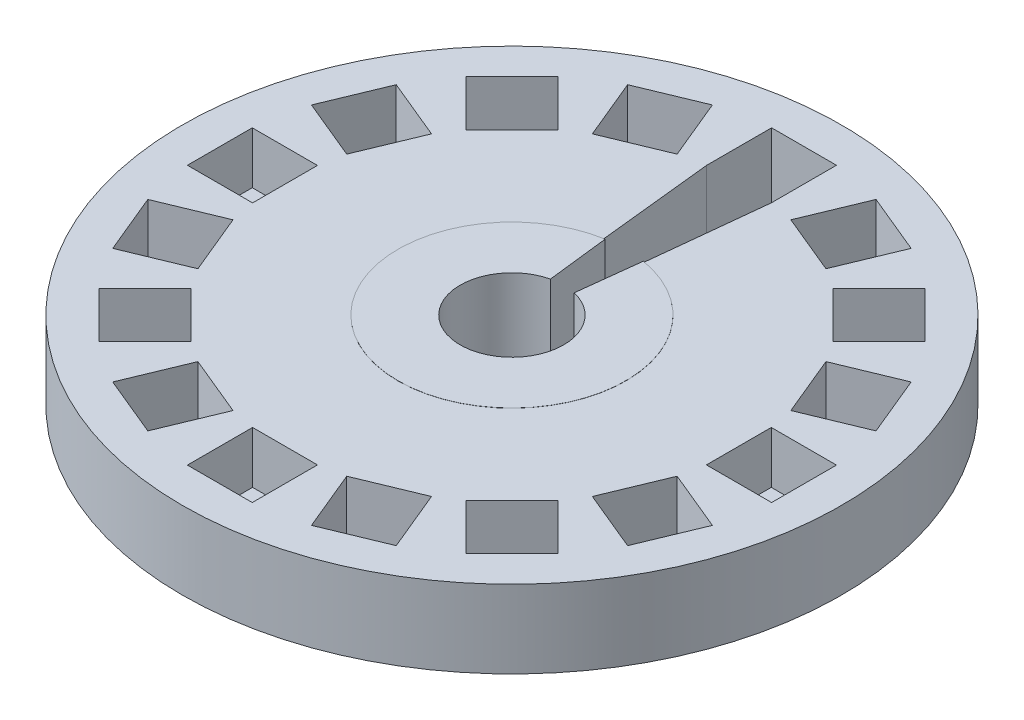
SolidWorks part; units mm, degrees
ref_plane "Front Plane" through (0, 0, 0) normal (0, 0, 1) x (1, 0, 0)
ref_plane "Top Plane" through (0, 0, 0) normal (0, 1, 0) x (1, 0, 0)
ref_plane "Right Plane" through (0, 0, 0) normal (1, 0, 0) x (0, 0, -1)
sketch "Sketch1" plane through (0, 0, 0) normal (0, 1, 0) x (1, 0, 0)
  circle A0 centre (0, 0) radius 63.5
  dimension "D1" = 127
extrude "Boss-Extrude1" add sketch "Sketch1" along normal blind 14.9734
sketch "Sketch2" plane through (0, 14.9734, 0) normal (0, 1, 0) x (1, 0, 0)
  line L0 (0, 0) -> (0, -50) construction
  line L1 (-6.25, -56.28) -> (6.25, -56.28)
  line L2 (-6.25, -56.28) -> (-6.25, -43.72)
  line L3 (-6.25, -43.72) -> (6.25, -43.72)
  line L4 (6.25, -56.28) -> (6.25, -43.72)
  line L5 (-6.25, -56.28) -> (6.25, -43.72) construction
  line L6 (-6.25, -43.72) -> (6.25, -56.28) construction
  point P0 (0, -50)
  dimension "D1" = 12.5
  dimension "D2" = 12.56
  dimension "D3" = 50
extrude "Cut-Extrude1" cut sketch "Sketch2" against normal blind 10
pattern_circular "CirPattern1" count 16 over 360 about axis through (0, 0, 0) along (0, 1, 0) of "Cut-Extrude1"
sketch "Sketch5" plane through (0, 0, 0) normal (0, 1, 0) x (1, 0, 0)
  line L0 (-56.28, 0) -> (-63.5, 0) construction
  line L1 (-56.28, 6.25) -> (-56.28, -6.25) construction
  line L3 (-6.25, 56.28) -> (6.25, 56.28)
  line L4 (-6.25, 56.28) -> (-6.25, 43.72)
  line L5 (-6.25, 43.72) -> (6.25, 43.72)
  line L6 (6.25, 56.28) -> (6.25, 43.72)
  circle A0 centre (0, 0) radius 63.5 construction
extrude "Cut-Extrude3" cut sketch "Sketch5" against normal blind 31 and the other way blind 37
sketch "Sketch6" plane through (0, 14.9734, 0) normal (0, 1, 0) x (1, 0, 0)
  circle A0 centre (0, 0) radius 17.6259
extrude "Cut-Extrude4" cut sketch "Sketch6" against normal blind 37 and the other way blind 26 contours A0
sketch "Sketch7" plane through (0, 0, 0) normal (0, 1, 0) x (1, 0, 0)
  line L5 (0, 43.72) -> (0, 0) construction
  line L6 (-6.25, 43.72) -> (6.25, 43.72) construction
sketch "Sketch8" plane through (0, 0, 0) normal (0, 1, 0) x (1, 0, 0)
sketch "Sketch9" plane through (0, 0, 0) normal (0, 1, 0) x (1, 0, 0)
  line L0 (-6.25, 43.72) -> (0, -15.0986)
  line L1 (0, -15.0986) -> (6.25, 43.72)
  line L2 (6.25, 43.72) -> (-6.25, 43.72)
extrude "Cut-Extrude9" cut sketch "Sketch9" against normal blind 11 and the other way blind 19
sketch "Sketch12" plane through (-6.25, 0, 0) normal (1, 0, 0) x (0, 0, -1)
  line L0 (56.28, 14.9734) -> (56.28, 9.9734) construction
  line L1 (56.28, 0) -> (56.28, 14.9734) construction
  line L2 (56.28, 9.9734) -> (18.4333, -3.0647)
  line L3 (18.4333, -3.0647) -> (18.4333, -10.1043)
  line L4 (18.4333, -10.1043) -> (54.4658, 0)
  line L5 (54.4658, 0) -> (56.28, 9.9734)
sketch "Sketch13" plane through (0, 0, 0) normal (0, 1, 0) x (1, 0, 0)
  circle A0 centre (0, 0) radius 21.9529
extrude "Boss-Extrude4" add sketch "Sketch13" against normal blind 18 and the other way blind 15
sketch "Sketch16" plane through (0, 0, 0) normal (0, 1, 0) x (1, 0, 0)
  circle A0 centre (0, 0) radius 9.9764
extrude "Cut-Extrude11" cut sketch "Sketch16" against normal blind 29 and the other way blind 33
sketch "Sketch17" plane through (0, 0, 0) normal (0, 1, 0) x (1, 0, 0)
  line L0 (-6.25, 43.72) -> (0, -9.9764)
  line L1 (-6.25, 56.28) -> (6.25, 56.28) construction
  line L2 (-6.25, 56.28) -> (-6.25, 43.72) construction
  line L3 (-6.25, 43.72) -> (6.25, 43.72) construction
  line L4 (6.25, 56.28) -> (6.25, 43.72) construction
  line L5 (-6.25, 56.28) -> (6.25, 43.72) construction
  line L6 (-6.25, 43.72) -> (6.25, 56.28) construction
  line L7 (0, -9.9764) -> (6.25, 43.72)
  line L8 (6.25, 43.72) -> (-6.25, 43.72)
  circle A0 centre (0, 0) radius 9.9764 construction
  point P4 (0, 50)
extrude "Cut-Extrude15" cut sketch "Sketch17" against normal blind 29 and the other way blind 27 contours L8 L0 L7
equation "\"line\"= 5"
equation "\"D3@Sketch2\"=\"line\""
